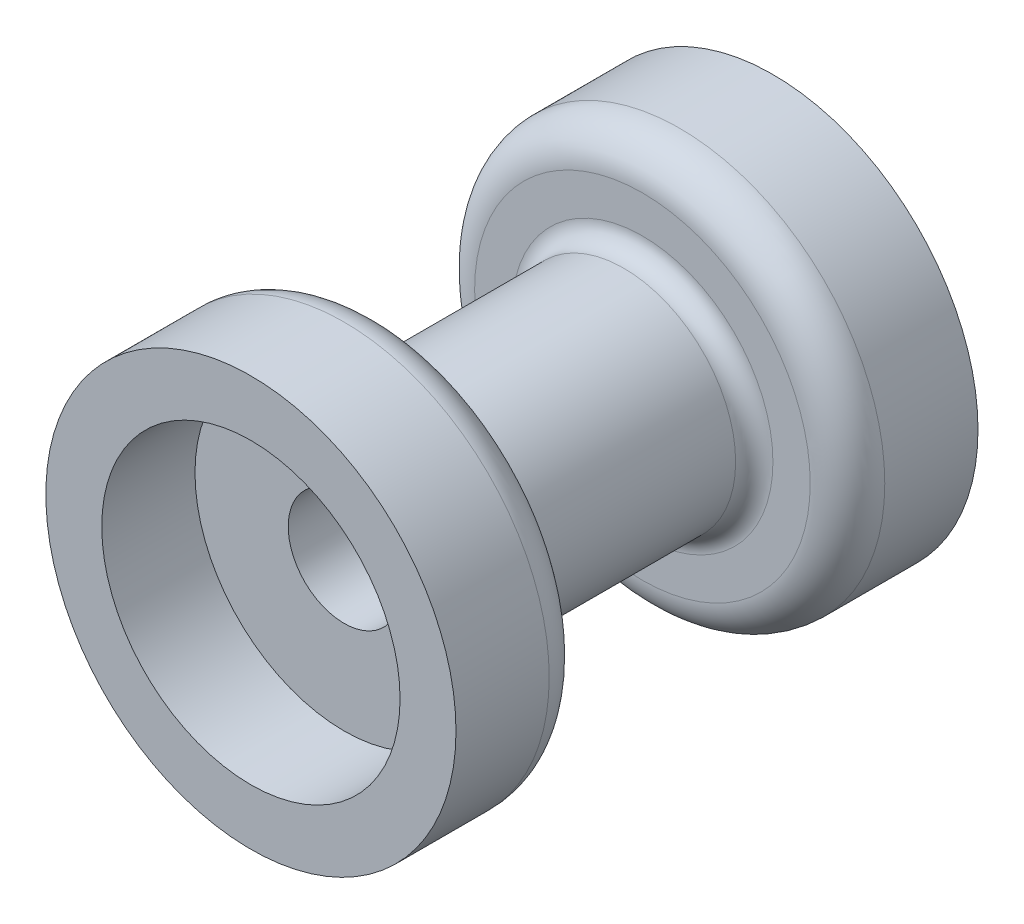
SolidWorks part; units mm, degrees
material "Nylon - impressão"
ref_plane "Plano frontal" through (0, 0, 0) normal (0, 0, 1) x (1, 0, 0)
ref_plane "Plano superior" through (0, 0, 0) normal (0, 1, 0) x (1, 0, 0)
ref_plane "Plano direito" through (0, 0, 0) normal (1, 0, 0) x (0, 0, -1)
sketch "Esboço1" plane through (0, 0, 0) normal (1, 0, 0) x (0, 0, -1)
  line L0 (0, 8) -> (0, 11)
  line L1 (0, 11) -> (5, 11)
  line L2 (7, 9) -> (7, 7)
  line L3 (8, 6) -> (20, 6)
  line L4 (21, 7) -> (21, 9)
  line L5 (23, 11) -> (28, 11)
  line L6 (28, 11) -> (28, 8)
  line L7 (28, 8) -> (23, 8)
  line L8 (23, 8) -> (23, 3)
  line L9 (23, 3) -> (5, 3)
  line L10 (5, 3) -> (5, 8)
  line L11 (5, 8) -> (0, 8)
  line L12 (0, 0) -> (51.2941, 0) construction
  arc A0 (21, 7) -> (20, 6) centre (20, 7) cw
  arc A1 (7, 7) -> (8, 6) centre (8, 7) ccw
  arc A2 (21, 9) -> (23, 11) centre (23, 9) cw
  arc A3 (7, 9) -> (5, 11) centre (5, 9) ccw
  point P17 (21, 6)
  point P20 (7, 6)
  point P25 (7, 11)
  dimension "D8" = 1
  dimension "D9" = 2
  dimension "D1" = 16
  dimension "D2" = 6
  dimension "D3" = 5
  dimension "D4" = 7
  dimension "D5" = 28
  dimension "D6" = 22
  dimension "D7" = 12
revolve "Revolução1" add sketch "Esboço1" angle 360 about L12
